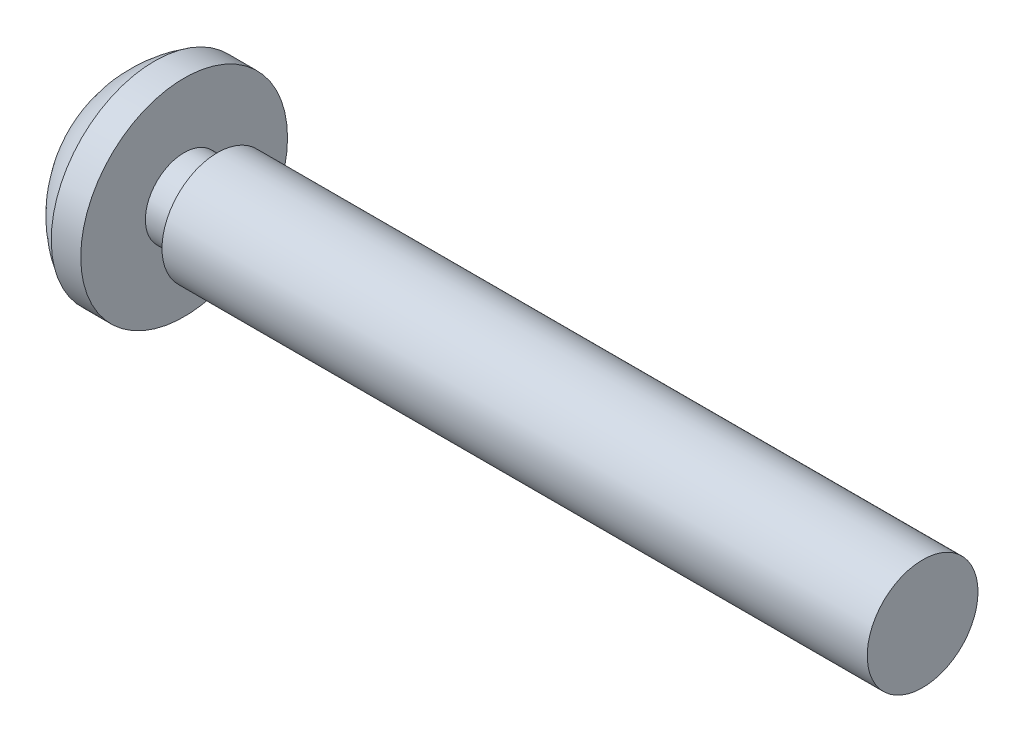
SolidWorks part; units mm, degrees
ref_plane "前视基准面" through (0, 0, 0) normal (0, 0, 1) x (1, 0, 0)
ref_plane "上视基准面" through (0, 0, 0) normal (0, 1, 0) x (1, 0, 0)
ref_plane "右视基准面" through (0, 0, 0) normal (1, 0, 0) x (0, 0, -1)
sketch "草图2" plane through (0, 0, 0) normal (0, 0, 1) x (1, 0, 0)
  line L0 (0, 0) -> (0, 1.5)
  line L1 (0, 1.5) -> (-19.1, 1.5)
  line L2 (-19.1, 1.5) -> (-19.1, 1.05)
  line L3 (-19.1, 1.05) -> (-20, 1.05)
  line L4 (-20, 1.05) -> (-20, 2.8)
  line L5 (-20, 2.8) -> (-20.8, 2.8)
  line L6 (0, 0) -> (-32.6437, 0) construction
  line L7 (0, 0) -> (-22.4, 0)
  arc A0 (-20.8, 2.8) -> (-22.4, 0) centre (-19.15, 0) ccw
  dimension "D1" = 3
  dimension "D2" = 20
  dimension "D3" = 0.8
  dimension "D4" = 2.4
  dimension "D5" = 5.6
  dimension "D8" = 0.9
  dimension "D9" = 0.45
revolve "旋转1" add sketch "草图2" angle 360 about L6
cosmetic thread "装饰螺纹线1" parameters "D2"=2.15
ref_plane "基准面1" through (-22.4, 0, 0) normal (1, 0, 0) x (0, 0, -1)
sketch "草图3" plane through (-22.4, 0, 0) normal (1, 0, 0) x (0, 0, -1)
  line L0 (0, 1.8) -> (0, -1.8) construction
  line L1 (0.375, 1.8) -> (-0.375, 1.8)
  line L2 (0.375, 1.8) -> (0.375, 0.675)
  line L3 (0.375, -1.8) -> (-0.375, -1.8)
  line L4 (-0.375, 1.8) -> (-0.375, 0.675)
  line L5 (-1.8, 0) -> (1.8, 0) construction
  line L6 (1.8, 0.375) -> (0.675, 0.375)
  line L7 (1.8, 0.375) -> (1.8, -0.375)
  line L8 (1.8, -0.375) -> (0.675, -0.375)
  line L9 (-1.8, 0.375) -> (-1.8, -0.375)
  line L10 (0.375, -0.675) -> (0.375, -1.8)
  line L11 (-0.675, 0.375) -> (-1.8, 0.375)
  line L12 (-0.375, -0.675) -> (-0.375, -1.8)
  line L13 (-0.675, -0.375) -> (-1.8, -0.375)
  arc A0 (-0.375, -0.675) -> (-0.675, -0.375) centre (-0.675, -0.675) ccw
  arc A1 (0.375, -0.675) -> (0.675, -0.375) centre (0.675, -0.675) cw
  arc A2 (0.675, 0.375) -> (0.375, 0.675) centre (0.675, 0.675) cw
  arc A3 (-0.375, 0.675) -> (-0.675, 0.375) centre (-0.675, 0.675) cw
  point P26 (0, 0)
  dimension "D3" = 0.3
  dimension "D1" = 0.75
  dimension "D2" = 3.6
extrude "切除-拉伸5" cut sketch "草图3" along normal blind 1.2
